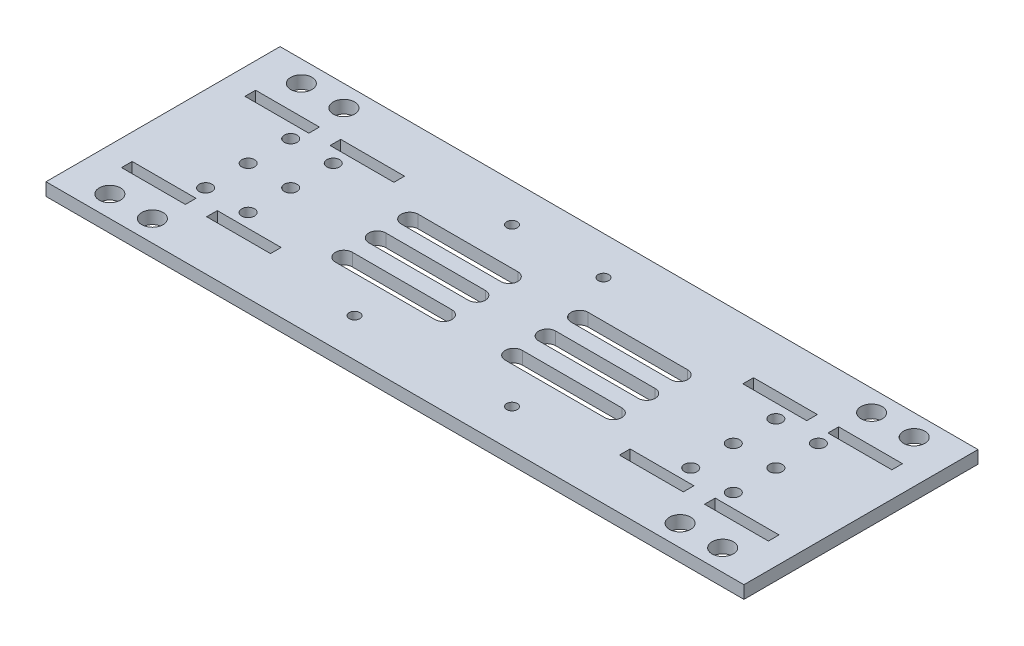
SolidWorks part; units mm, degrees
ref_plane "Front Plane" through (0, 0, 0) normal (0, 0, 1) x (1, 0, 0)
ref_plane "Top Plane" through (0, 0, 0) normal (0, 1, 0) x (1, 0, 0)
ref_plane "Right Plane" through (0, 0, 0) normal (1, 0, 0) x (0, 0, -1)
sketch "Sketch1" plane through (0, 0, 0) normal (0, 1, 0) x (1, 0, 0)
  line L0 (0, -5.7309) -> (0, 9.5321) construction
  line L1 (82, 27.5) -> (-82, 27.5)
  line L2 (82, 27.5) -> (82, -27.5)
  line L3 (82, -27.5) -> (-82, -27.5)
  line L4 (-82, 27.5) -> (-82, -27.5)
  line L6 (56, 15.75) -> (41, 15.75)
  line L7 (56, 15.75) -> (56, 13.25)
  line L8 (56, 13.25) -> (41, 13.25)
  line L9 (41, 15.75) -> (41, 13.25)
  line L10 (76, 15.75) -> (61, 15.75)
  line L11 (76, 15.75) -> (76, 13.25)
  line L12 (76, 13.25) -> (61, 13.25)
  line L13 (61, 15.75) -> (61, 13.25)
  line L15 (-7.975, 0) -> (11.9988, 0) construction
  line L19 (61, -15.75) -> (61, -13.25)
  line L20 (76, -13.25) -> (61, -13.25)
  line L21 (76, -15.75) -> (76, -13.25)
  line L22 (76, -15.75) -> (61, -15.75)
  line L23 (41, -15.75) -> (41, -13.25)
  line L24 (56, -13.25) -> (41, -13.25)
  line L25 (56, -15.75) -> (56, -13.25)
  line L26 (56, -15.75) -> (41, -15.75)
  line L28 (-56, -15.75) -> (-41, -15.75)
  line L29 (-56, -15.75) -> (-56, -13.25)
  line L30 (-56, -13.25) -> (-41, -13.25)
  line L31 (-41, -15.75) -> (-41, -13.25)
  line L32 (-76, -15.75) -> (-61, -15.75)
  line L33 (-76, -15.75) -> (-76, -13.25)
  line L34 (-76, -13.25) -> (-61, -13.25)
  line L35 (-61, -15.75) -> (-61, -13.25)
  line L40 (-61, 15.75) -> (-61, 13.25)
  line L41 (-76, 13.25) -> (-61, 13.25)
  line L42 (-76, 15.75) -> (-76, 13.25)
  line L43 (-76, 15.75) -> (-61, 15.75)
  line L44 (-41, 15.75) -> (-41, 13.25)
  line L45 (-56, 13.25) -> (-41, 13.25)
  line L46 (-56, 15.75) -> (-56, 13.25)
  line L47 (-56, 15.75) -> (-41, 15.75)
  dimension "D4" = 2.5
  dimension "D5" = 15
  dimension "D6" = 15
  dimension "D7" = 2.5
  dimension "D10" = 164
  dimension "D11" = 82
  dimension "D12" = 55
  dimension "D13" = 27.5
  dimension "D20" = 2.5
extrude "Boss-Extrude1" add sketch "Sketch1" along normal blind 3
sketch "Sketch2" plane through (0, 3, 0) normal (0, 1, 0) x (1, 0, 0)
  line L0 (-31.6585, 2) -> (-8.2664, 2)
  line L1 (31.6585, -9.8567) -> (8.2664, -9.8567)
  line L2 (31.6585, -5.8567) -> (8.2664, -5.8567)
  line L4 (-31.6585, -2) -> (-8.2664, -2)
  line L5 (-31.6585, 9.6208) -> (-8.2664, 9.6208)
  line L6 (-31.6585, 5.6208) -> (-8.2664, 5.6208)
  line L7 (31.6585, 5.6208) -> (8.2664, 5.6208)
  line L8 (31.6585, 9.6208) -> (8.2664, 9.6208)
  line L9 (-31.6585, -5.8567) -> (-8.2664, -5.8567)
  line L10 (31.6585, -2) -> (8.2664, -2)
  line L11 (31.6585, 2) -> (8.2664, 2)
  line L12 (-31.6585, -9.8567) -> (-8.2664, -9.8567)
  line L15 (0, 0) -> (-4.1634, 0) construction
  arc A0 (31.6585, -9.8567) -> (31.6585, -5.8567) centre (31.6585, -7.8567) ccw
  arc A1 (8.2664, -5.8567) -> (8.2664, -9.8567) centre (8.2664, -7.8567) ccw
  arc A2 (-8.2664, 2) -> (-8.2664, -2) centre (-8.2664, 0) cw
  arc A3 (-31.6585, -2) -> (-31.6585, 2) centre (-31.6585, 0) cw
  arc A4 (31.6585, 5.6208) -> (31.6585, 9.6208) centre (31.6585, 7.6208) ccw
  arc A5 (8.2664, 9.6208) -> (8.2664, 5.6208) centre (8.2664, 7.6208) ccw
  arc A6 (31.6585, -2) -> (31.6585, 2) centre (31.6585, 0) ccw
  arc A7 (8.2664, 2) -> (8.2664, -2) centre (8.2664, 0) ccw
  arc A8 (-8.2664, 9.6208) -> (-8.2664, 5.6208) centre (-8.2664, 7.6208) cw
  arc A9 (-31.6585, 5.6208) -> (-31.6585, 9.6208) centre (-31.6585, 7.6208) cw
  arc A10 (-8.2664, -5.8567) -> (-8.2664, -9.8567) centre (-8.2664, -7.8567) cw
  arc A11 (-31.6585, -9.8567) -> (-31.6585, -5.8567) centre (-31.6585, -7.8567) cw
extrude "Cut-Extrude1" cut sketch "Sketch2" against normal blind 3
sketch "Sketch3" plane through (0, 3, 0) normal (0, 1, 0) x (1, 0, 0)
  circle A0 centre (18.5, -18.5) radius 1.25
  circle A1 centre (-18.5, -18.5) radius 1.25
  circle A2 centre (-18.5, 18.5) radius 1.25
  circle A3 centre (3, 18.5) radius 1.25
  dimension "D1" = 18.5
  dimension "D2" = 3
  dimension "D3" = 2.5
  dimension "D4" = 2.5
  dimension "D5" = 2.5
  dimension "D6" = 2.5
extrude "Cut-Extrude2" cut sketch "Sketch3" against normal blind 10
sketch "Sketch4" plane through (0, 3, 0) normal (0, 1, 0) x (1, 0, 0)
  line L16 (82, -27.5) -> (82, 27.5) construction
  line L26 (-82, -27.5) -> (82, -27.5) construction
  line L30 (63.8385, 0) -> (72.3938, 0) construction
  line L31 (-82, 27.5) -> (-82, -27.5) construction
  line L34 (82, 27.5) -> (-82, 27.5) construction
  circle A0 centre (72, -22.5) radius 2.5
  circle A1 centre (62, -22.5) radius 2.5
  circle A2 centre (72, 22.5) radius 2.5
  circle A3 centre (62, 22.5) radius 2.5
  circle A4 centre (-72, 22.5) radius 2.5
  circle A5 centre (-62, 22.5) radius 2.5
  circle A6 centre (-72, -22.5) radius 2.5
  circle A7 centre (-62, -22.5) radius 2.5
  point P0 (-78, 0)
  point P1 (0, 0)
  point P7 (-59, 0)
  point P15 (78, 0)
  point P24 (78, 0)
  dimension "D3" = 10
  dimension "D5" = 5
  dimension "D7" = 10
  dimension "D8" = 5
  dimension "D9" = 5
  dimension "D10" = 5
  dimension "D11" = 10
  dimension "D12" = 5
  dimension "D13" = 10
  dimension "D14" = 5
  dimension "D15" = 5
  dimension "D16" = 5
  dimension "D17" = 5
  dimension "D18" = 5
  dimension "D19" = 10
  dimension "D20" = 10
  dimension "D21" = 5
  dimension "D22" = 5
extrude "Cut-Extrude3" cut sketch "Sketch4" against normal through all
sketch "Sketch5" plane through (0, 0, 0) normal (0, -1, 0) x (1, 0, 0)
  circle A0 centre (52, 10) radius 1.5
  circle A1 centre (62, 10) radius 1.5
  circle A2 centre (62, 0) radius 1.5
  circle A3 centre (52, 0) radius 1.5
  circle A4 centre (52, -10) radius 1.5
  circle A5 centre (62, -10) radius 1.5
  circle A6 centre (-52, 10) radius 1.5
  circle A7 centre (-52, 0) radius 1.5
  circle A8 centre (-52, -10) radius 1.5
  circle A9 centre (-62, 10) radius 1.5
  circle A10 centre (-62, 0) radius 1.5
  circle A11 centre (-62, -10) radius 1.5
extrude "Cut-Extrude4" cut sketch "Sketch5" against normal blind 10
